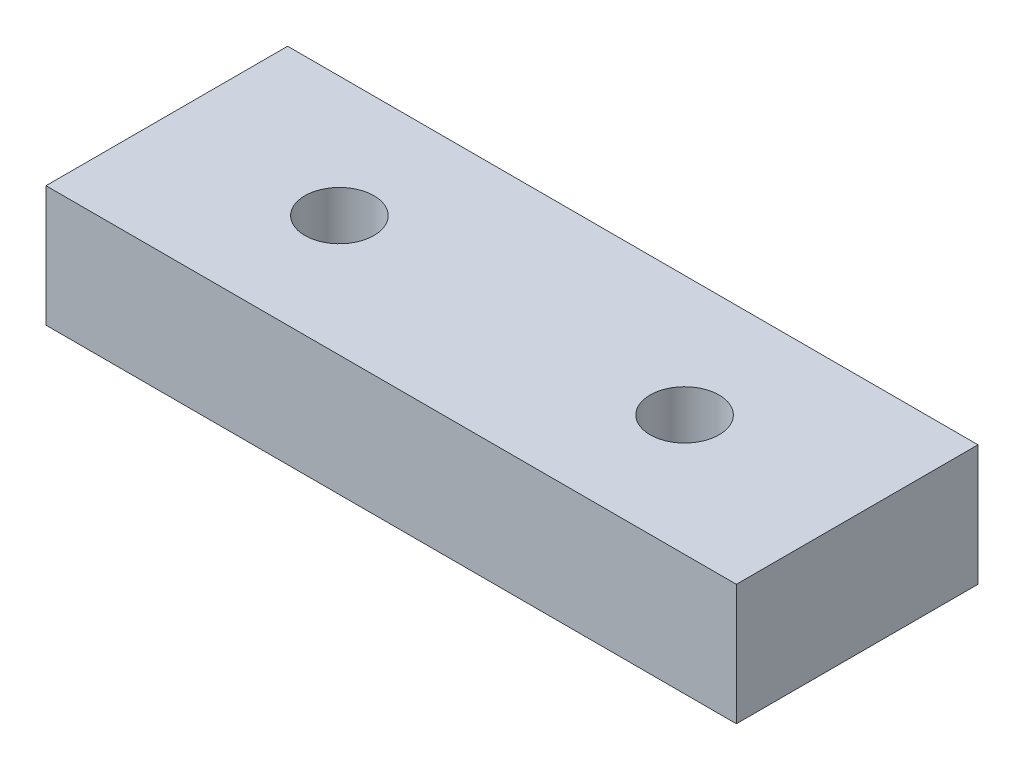
SolidWorks part; units mm, degrees
ref_plane "Alzado" through (0, 0, 0) normal (0, 0, 1) x (1, 0, 0)
ref_plane "Planta" through (0, 0, 0) normal (0, 1, 0) x (1, 0, 0)
ref_plane "Vista lateral" through (0, 0, 0) normal (1, 0, 0) x (0, 0, -1)
sketch "Croquis1" plane through (0, 0, 0) normal (0, 1, 0) x (1, 0, 0)
  line L1 (0, 0) -> (20, 0)
  line L2 (0, 0) -> (0, 7)
  line L3 (0, 7) -> (20, 7)
  line L4 (20, 0) -> (20, 7)
  circle A0 centre (5, 3.5) radius 1
  circle A1 centre (15, 3.5) radius 1
  point P9 (0, 0)
  dimension "D3" = 2
  dimension "D1" = 7
  dimension "D2" = 20
  dimension "D4" = 5
  dimension "D5" = 5
  dimension "D6" = 3.5
extrude "Saliente-Extruir1" add sketch "Croquis1" along normal blind 3.5
